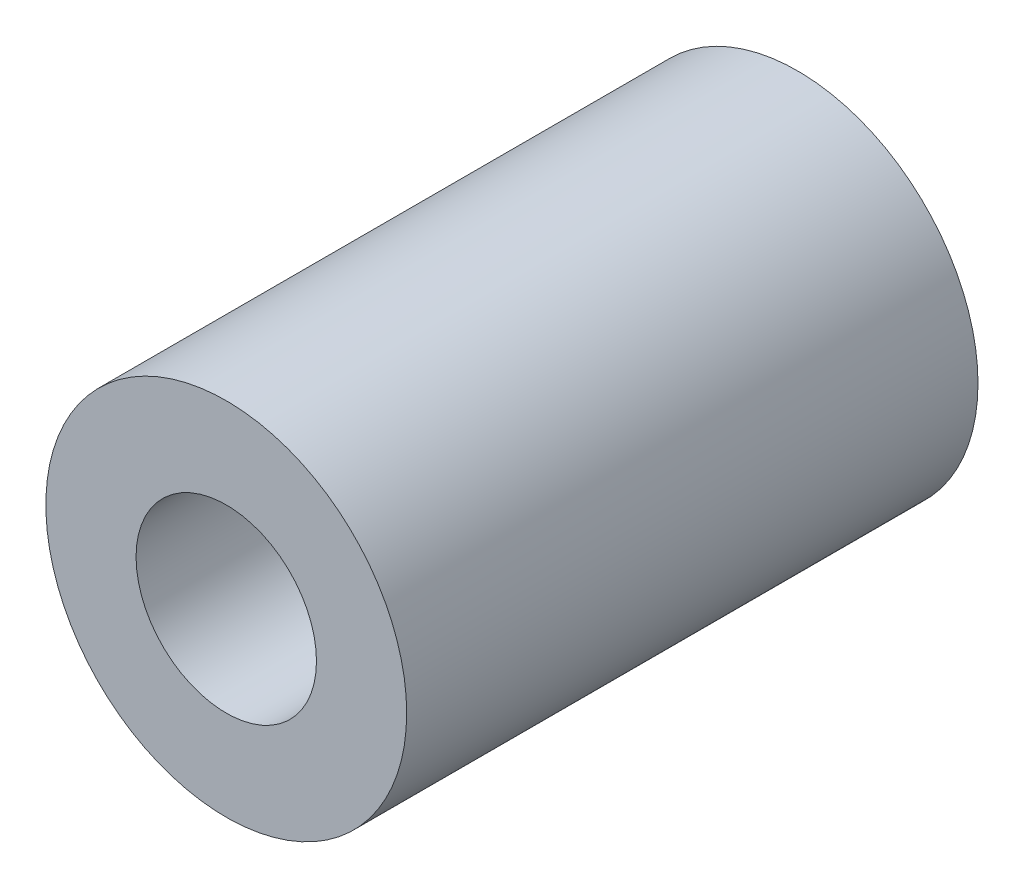
SolidWorks part; units mm, degrees
ref_plane "正面" through (0, 0, 0) normal (0, 0, 1) x (1, 0, 0)
ref_plane "平面" through (0, 0, 0) normal (0, 1, 0) x (1, 0, 0)
ref_plane "右側面" through (0, 0, 0) normal (1, 0, 0) x (0, 0, -1)
sketch "ｽｹｯﾁ1" plane through (0, 0, 0) normal (0, 0, 1) x (1, 0, 0)
  circle A0 centre (0, 0) radius 3
  circle A1 centre (0, 0) radius 6
  dimension "D1" = 6
  dimension "D2" = 12
extrude "ﾎﾞｽ - 押し出し1" add sketch "ｽｹｯﾁ1" along normal blind 19
